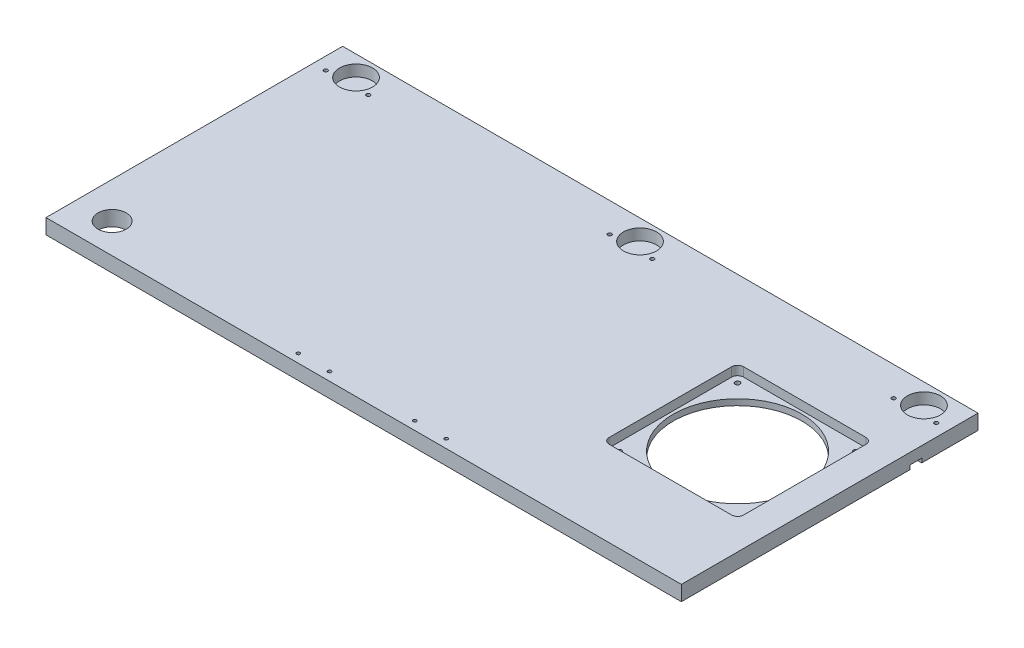
SolidWorks part; units mm, degrees
ref_plane "Front Plane" through (0, 0, 0) normal (0, 0, 1) x (1, 0, 0)
ref_plane "Top Plane" through (0, 0, 0) normal (0, 1, 0) x (1, 0, 0)
ref_plane "Right Plane" through (0, 0, 0) normal (1, 0, 0) x (0, 0, -1)
sketch "Sketch1" plane through (0, 0, 0) normal (0, 1, 0) x (1, 0, 0)
  line L1 (335.6356, 156.7053) -> (-335.6356, 156.7053)
  line L2 (335.6356, 156.7053) -> (335.6356, -156.7053)
  line L3 (335.6356, -156.7053) -> (-335.6356, -156.7053)
  line L4 (-335.6356, 156.7053) -> (-335.6356, -156.7053)
  line L5 (335.6356, 156.7053) -> (-335.6356, -156.7053) construction
  line L6 (335.6356, -156.7053) -> (-335.6356, 156.7053) construction
  point P0 (0, 0)
  dimension "D1" = 671.2712
  dimension "D2" = 313.4106
extrude "Boss-Extrude1" add sketch "Sketch1" along normal blind 15.875
sketch "Sketch2" plane through (0, 15.875, 0) normal (0, 1, 0) x (1, 0, 0)
  line L0 (335.6356, 156.7053) -> (-335.6356, 156.7053) construction
  line L1 (343.5731, 137.6553) -> (-343.5731, 137.6553)
  line L2 (343.5731, 137.6553) -> (343.5731, -137.6553)
  line L3 (343.5731, -137.6553) -> (-343.5731, -137.6553)
  line L4 (-343.5731, 137.6553) -> (-343.5731, -137.6553)
  line L5 (343.5731, 137.6553) -> (-343.5731, -137.6553) construction
  line L6 (343.5731, -137.6553) -> (-343.5731, 137.6553) construction
  line L7 (-335.6356, 156.7053) -> (-335.6356, -156.7053) construction
  point P0 (0, 0)
  dimension "D1" = 19.05
  dimension "D2" = 7.9375
extrude "Boss-Extrude2" [suppressed] add sketch "Sketch2" against normal up to surface (15.875 mm away)
fillet "Fillet1" [suppressed] radius 6.35
sketch "Sketch4" plane through (0, 15.875, 0) normal (0, 1, 0) x (1, 0, 0)
  line L1 (0, 0) -> (0, -124.9553) construction
  line L2 (-335.6356, -156.7053) -> (335.6356, -156.7053) construction
  line L3 (-335.6356, 156.7053) -> (-335.6356, -156.7053) construction
  circle A1 centre (-297.5356, -124.9553) radius 14.9225
  dimension "D3" = 31.75
  dimension "D5" = 29.845
  dimension "D4" = 38.1
extrude "Cut-Extrude2" cut sketch "Sketch4" against normal through all both and the other way through all
sketch "Sketch5" plane through (0, 15.875, 0) normal (0, 1, 0) x (1, 0, 0)
  line L0 (0, 0) -> (0, 156.7053) construction
  line L1 (335.6356, 156.7053) -> (-335.6356, 156.7053) construction
  line L2 (-300, 135.2428) -> (-300, 146.2735) construction
  circle A0 centre (0, 135.2428) radius 17.4625
  circle A1 centre (22.5, 125.7428) radius 2
  circle A2 centre (-22.5, 125.7428) radius 2
  circle A3 centre (-300, 135.2428) radius 17.4625
  circle A4 centre (-277.5, 125.7428) radius 2
  circle A5 centre (-322.5, 125.7428) radius 2
  circle A6 centre (322.5, 125.7428) radius 2
  circle A7 centre (277.5, 125.7428) radius 2
  circle A8 centre (300, 135.2428) radius 17.4625
  dimension "D1" = 34.925
  dimension "D3" = 45
  dimension "D4" = 4
  dimension "D6" = 4
  dimension "D5" = 9.5
  dimension "D2" = 45
  dimension "D7" = 300
extrude "Cut-Extrude3" cut sketch "Sketch5" against normal blind 11.9062
sketch "Sketch6" plane through (0, 15.875, 0) normal (0, 1, 0) x (1, 0, 0)
  line L0 (-335.6356, -156.7053) -> (335.6356, -156.7053) construction
  line L1 (78.05, -147.7053) -> (45.05, -147.7053) construction
  line L2 (-45.05, -147.7053) -> (-78.05, -147.7053) construction
  circle A0 centre (78.05, -147.7053) radius 1.8
  circle A1 centre (45.05, -147.7053) radius 1.8
  circle A2 centre (-45.05, -147.7053) radius 1.8
  circle A4 centre (-78.05, -147.7053) radius 1.8
  point P8 (61.55, -147.7053)
  point P12 (-61.55, -147.7053)
  dimension "D2" = 3.6
  dimension "D3" = 33
  dimension "D1" = 9
  dimension "D4" = 33
  dimension "D5" = 61.55
  dimension "D6" = 61.55
extrude "Cut-Extrude4" cut sketch "Sketch6" against normal blind 2.54
sketch "Sketch7" plane through (0, 15.875, 0) normal (0, 1, 0) x (1, 0, 0)
  line L2 (335.6356, 156.7053) -> (-335.6356, 156.7053) construction
  line L3 (335.6356, -156.7053) -> (335.6356, 156.7053) construction
  circle A0 centre (234.0356, 4.3053) radius 68
  circle A1 centre (296.5356, -58.1947) radius 2.54
  circle A2 centre (296.5356, 66.8053) radius 2.54
  circle A3 centre (171.5356, 66.8053) radius 2.54
  circle A4 centre (171.5356, -58.1947) radius 2.54
  circle A5 centre (234.0356, 4.3053) radius 88.3883 construction
  dimension "D1" = 125
  dimension "D2" = 125
  dimension "D3" = 5.08
  dimension "D4" = 136
  dimension "D5" = 152.4
  dimension "D6" = 101.6
extrude "Cut-Extrude5" cut sketch "Sketch7" against normal through all both and the other way through all
sketch "Sketch8" plane through (0, 15.875, 0) normal (0, 1, 0) x (1, 0, 0)
  line L1 (169.3856, -66.6947) -> (298.6856, -66.6947)
  line L2 (163.0356, -60.3447) -> (163.0356, 68.9553)
  line L3 (169.3856, 75.3053) -> (298.6856, 75.3053)
  line L4 (305.0356, -60.3447) -> (305.0356, 68.9553)
  line L5 (163.0356, -66.6947) -> (305.0356, 75.3053) construction
  line L6 (163.0356, 75.3053) -> (305.0356, -66.6947) construction
  arc A0 (163.0356, 68.9553) -> (169.3856, 75.3053) centre (169.3856, 68.9553) cw
  arc A1 (298.6856, 75.3053) -> (305.0356, 68.9553) centre (298.6856, 68.9553) cw
  arc A2 (298.6856, -66.6947) -> (305.0356, -60.3447) centre (298.6856, -60.3447) ccw
  arc A3 (169.3856, -66.6947) -> (163.0356, -60.3447) centre (169.3856, -60.3447) cw
  point P0 (234.0356, 4.3053)
  dimension "D3" = 6.35
  dimension "D1" = 142
  dimension "D2" = 142
extrude "Cut-Extrude6" cut sketch "Sketch8" against normal blind 9.525
sketch "Sketch9" plane through (0, 0, 0) normal (0, -1, 0) x (1, 0, 0)
  line L0 (335.6356, 156.7053) -> (335.6356, -156.7053) construction
  line L1 (335.6356, -97.2947) -> (-335.6356, -97.2947)
  line L2 (335.6356, -97.2947) -> (335.6356, -84.7947)
  line L3 (335.6356, -84.7947) -> (-335.6356, -84.7947)
  line L4 (-335.6356, -97.2947) -> (-335.6356, -84.7947)
  line L5 (-335.6356, -156.7053) -> (-335.6356, 156.7053) construction
  line L6 (-335.6356, 156.7053) -> (335.6356, 156.7053) construction
  dimension "D1" = 12.5
  dimension "D2" = 254
extrude "Cut-Extrude7" cut sketch "Sketch9" against normal blind 4.35
